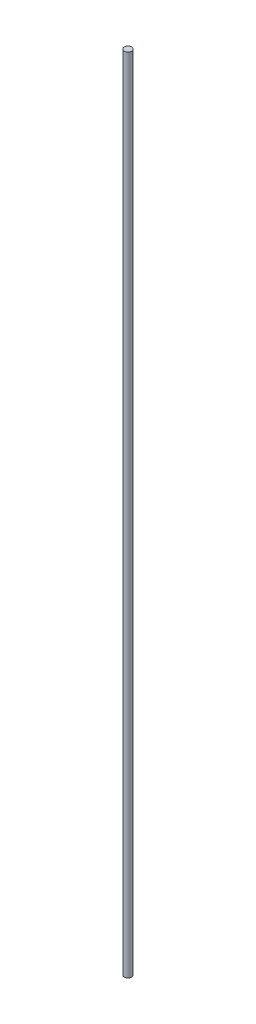
SolidWorks part; units mm, degrees
ref_plane "Front Plane" through (0, 0, 0) normal (0, 0, 1) x (1, 0, 0)
ref_plane "Top Plane" through (0, 0, 0) normal (0, 1, 0) x (1, 0, 0)
ref_plane "Right Plane" through (0, 0, 0) normal (1, 0, 0) x (0, 0, -1)
sketch "Sketch1" plane through (0, 0, 0) normal (0, 1, 0) x (1, 0, 0)
  circle A0 centre (0, 0) radius 3.175
  dimension "D1" = 6.35
extrude "Boss-Extrude1" add sketch "Sketch1" along normal mid plane 685.8
